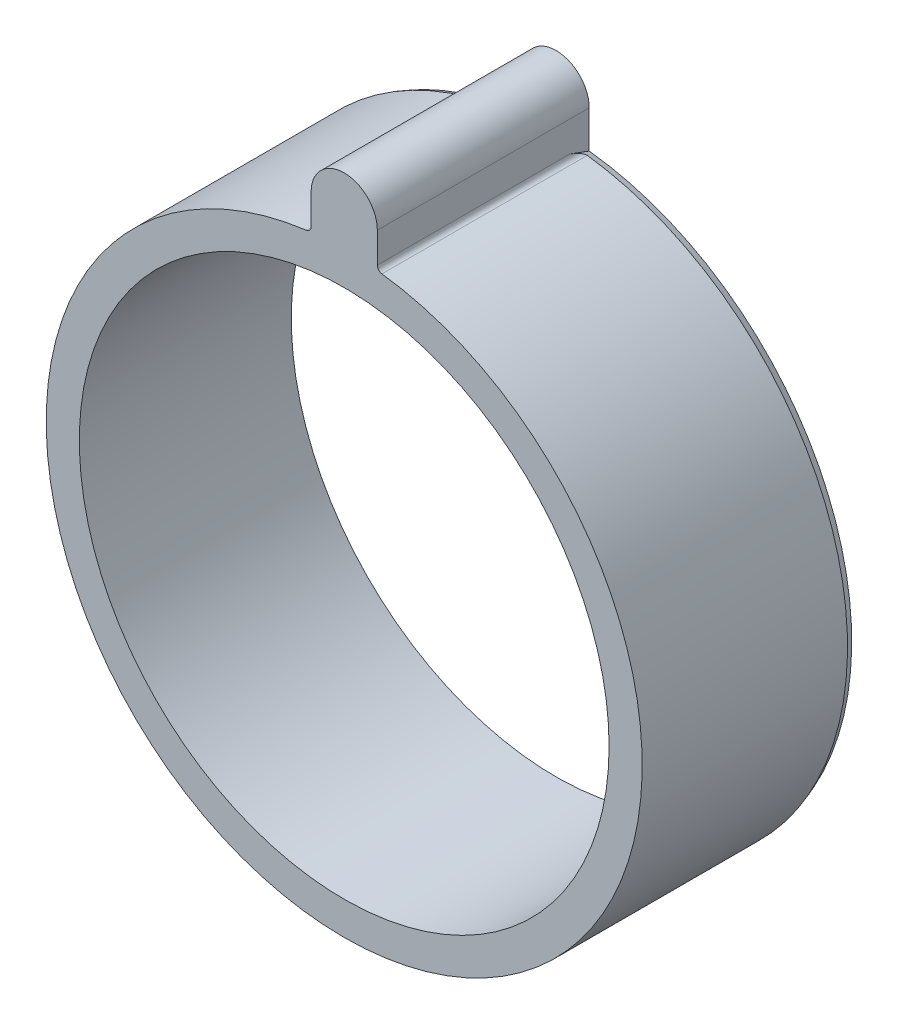
SolidWorks part; units mm, degrees
ref_plane "Plane1" through (0, 0, 0) normal (0, 0, 1) x (1, 0, 0)
ref_plane "Plane2" through (0, 0, 0) normal (0, 1, 0) x (1, 0, 0)
ref_plane "Plane3" through (0, 0, 0) normal (1, 0, 0) x (0, 0, -1)
sketch "Sketch1" plane through (0, 0, 0) normal (0, 0, 1) x (1, 0, 0)
  circle A0 centre (0, 0) radius 20
  circle A1 centre (0, 0) radius 22.5
  dimension "D1" = 40
  dimension "D2" = 45
extrude "Extrude1" add sketch "Sketch1" along normal blind 16
sketch "Sketch3" plane through (0, 0, 16) normal (0, 0, 1) x (1, 0, 0)
  line L0 (0, 0) -> (0, 25) construction
  line L2 (2.5, 25) -> (2.5, 22.3607)
  line L3 (-2.5, 25) -> (-2.5, 22.3607)
  circle A0 centre (0, 0) radius 22.5 construction
  arc A1 (2.5, 22.3607) -> (-2.5, 22.3607) centre (0, 0) ccw
  arc A2 (-2.5, 25) -> (2.5, 25) centre (0, 25) cw
  dimension "D1" = 5
  dimension "D2" = 25
extrude "Extrude2" add sketch "Sketch3" against normal up to surface (16 mm away) up to face at (22.5, 0, 0)
chamfer "Chamfer1" distance 0.5 angle 20 1 edges at (0, -22.5, 0)
fillet "Fillet1" radius 0.4 2 edges at (2.5, 22.3607, 8.25) (-2.5, 22.3607, 8.25)
